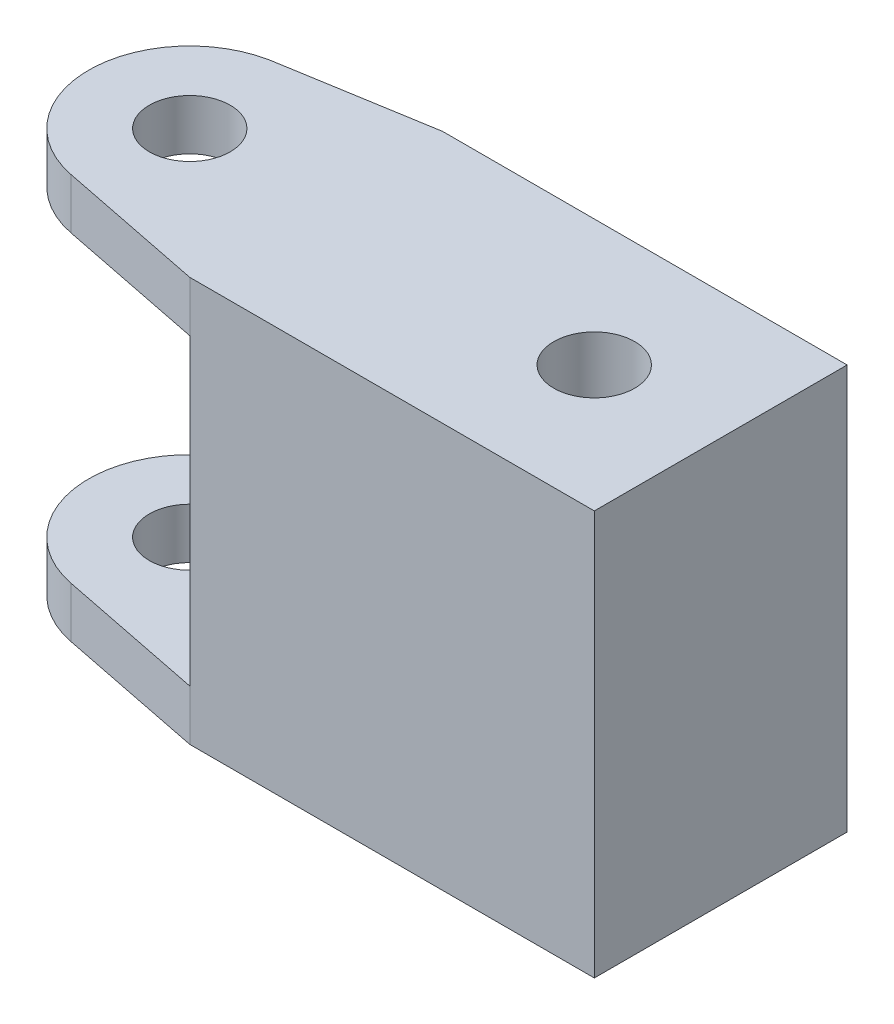
SolidWorks part; units mm, degrees
ref_plane "Plan de face" through (0, 0, 0) normal (0, 0, 1) x (1, 0, 0)
ref_plane "Plan de dessus" through (0, 0, 0) normal (0, 1, 0) x (1, 0, 0)
ref_plane "Plan de droite" through (0, 0, 0) normal (1, 0, 0) x (0, 0, -1)
sketch "Esquisse1" plane through (0, 0, 0) normal (0, 0, 1) x (1, 0, 0)
  line L1 (-20, 20) -> (20, 20)
  line L2 (-20, 20) -> (-20, -20)
  line L3 (-20, -20) -> (20, -20)
  line L4 (20, 20) -> (20, -20)
  line L5 (-20, 20) -> (20, -20) construction
  line L6 (-20, -20) -> (20, 20) construction
  point P0 (0, 0)
  dimension "D1" = 40
  dimension "D2" = 40
extrude "Boss.-Extru.1" add sketch "Esquisse1" along normal blind 25
sketch "Esquisse2" plane through (0, 20, 0) normal (0, 1, 0) x (1, 0, 0)
  line L0 (20, -12.5) -> (-5.0141, -12.5) construction
  line L1 (20, -25) -> (20, 0) construction
  circle A0 centre (7.4929, -12.5) radius 4
  dimension "D1" = 8
extrude "Enlèv. mat.-Extru.1" cut sketch "Esquisse2" against normal blind 47
ref_plane "Plan3" through (0, 20, 0) normal (0, 1, 0) x (1, 0, 0)
sketch "Esquisse4" plane through (0, 20, 0) normal (0, 1, 0) x (1, 0, 0)
  line L0 (-20, -25) -> (-34.7093, -22.061)
  line L1 (-20, 0) -> (-34.7093, -2.4487)
  line L2 (-20, -25) -> (-20, 0)
  line L3 (-20, -25) -> (-20, 0) construction
  line L4 (-34.7093, -22.061) -> (-34.7093, -2.4487) construction
  arc A0 (-34.7093, -22.061) -> (-34.7093, -2.4487) centre (-32.7499, -12.2548) cw
  circle A1 centre (-32.7499, -12.2548) radius 4
  dimension "D1" = 8
  dimension "D3" = 10
  dimension "D2" = 15
extrude "Boss.-Extru.3" add sketch "Esquisse4" against normal blind 5
mirror "Symétrie2" about plane through (0, 0, 0) normal (0, 1, 0) of "Boss.-Extru.3"
